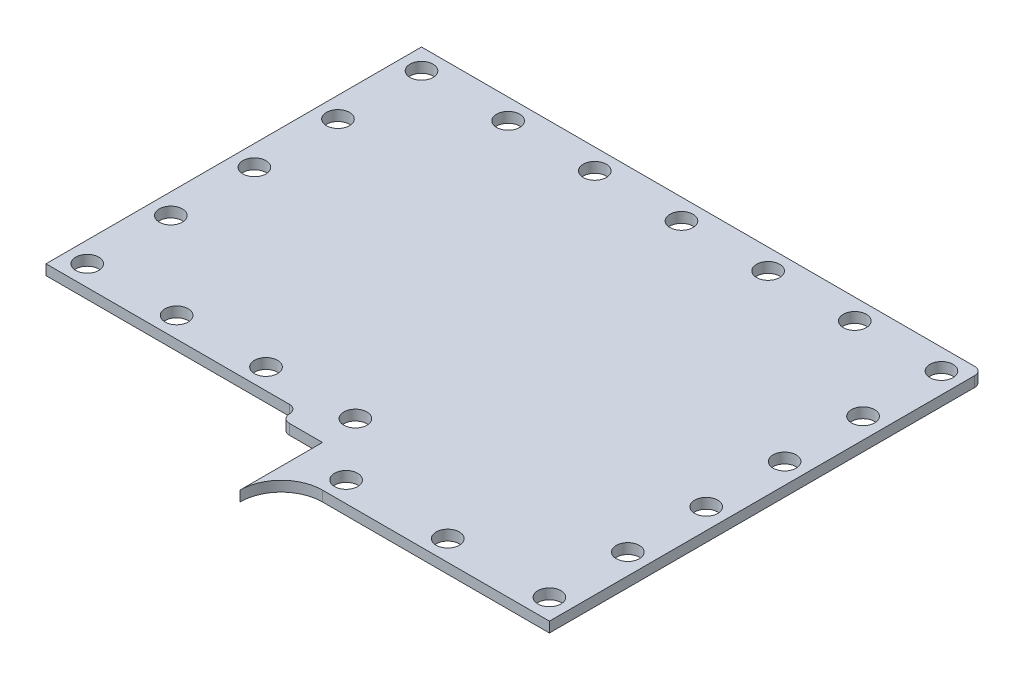
SolidWorks part; units mm, degrees
material "Zoltek Panex 33"
ref_plane "Front Plane" through (0, 0, 0) normal (0, 0, 1) x (1, 0, 0)
ref_plane "Top Plane" through (0, 0, 0) normal (0, 1, 0) x (1, 0, 0)
ref_plane "Right Plane" through (0, 0, 0) normal (1, 0, 0) x (0, 0, -1)
other "Bounding Box"
ref_plane "Default Plane" through (-8.9266, -12.7485, 0) normal (-0.1736, 0.9848, 0) x (0.9848, 0.1736, 0)
sketch "Sketch1" plane through (0, 0, 0) normal (0, 1, 0) x (1, 0, 0)
  line B0 (8.89, -66.675) -> (43.815, -66.675)
  line B1 (43.815, -66.675) -> (43.815, -1.27)
  line B2 (42.545, 0) -> (-42.545, 0)
  line B3 (-42.545, 0) -> (-42.545, -57.785)
  line B4 (-42.545, -57.785) -> (-5.08, -57.785)
  line B5 (-2.54, -60.325) -> (2.54, -60.325)
  line B6 (2.54, -60.325) -> (2.54, -73.025)
  arc B7 (8.89, -66.675) -> (2.54, -73.025) centre (8.89, -73.025) ccw
  arc B8 (43.815, -1.27) -> (42.545, 0) centre (42.5797, -1.2353) ccw
  arc B9 (-5.08, -57.785) -> (-3.81, -59.055) centre (-5.08, -59.055) cw
  arc B10 (-3.81, -59.055) -> (-2.54, -60.325) centre (-2.54, -59.055) ccw
sketch_block_instance "Left side Top plate-1"
sketch_block "Left side Top plate"
extrude "Boss-Extrude1" add sketch "Sketch1" along normal blind 1.5875
sketch "Sketch2" plane through (0, 1.5875, 0) normal (0, 1, 0) x (-1, 0, 0)
  line L0 (-9.3488, 63.5) -> (-40.64, 63.5) construction
  line L1 (-40.64, 63.5) -> (-40.64, 3.175) construction
  line L2 (-40.64, 3.175) -> (39.37, 3.175) construction
  line L3 (39.37, 3.175) -> (39.37, 54.61) construction
  line L4 (39.37, 54.61) -> (-1.8892, 54.61) construction
  line L5 (-1.8892, 54.61) -> (-9.3488, 63.5) construction
  line L6 (-42.545, 0) -> (42.545, 0) construction
  line L7 (42.545, 0) -> (42.545, 57.785) construction
  line L8 (42.545, 57.785) -> (5.08, 57.785) construction
  line L9 (-8.89, 66.675) -> (-43.815, 66.675) construction
  line L10 (-43.815, 66.675) -> (-43.815, 1.27) construction
  circle A0 centre (39.37, 3.175) radius 1.778
  circle A1 centre (26.035, 3.175) radius 1.778
  circle A2 centre (12.7, 3.175) radius 1.778
  circle A3 centre (-0.635, 3.175) radius 1.778
  circle A4 centre (-13.97, 3.175) radius 1.778
  circle A5 centre (-27.305, 3.175) radius 1.778
  circle A6 centre (-40.64, 3.175) radius 1.778
  circle A7 centre (39.37, 16.0338) radius 1.778
  circle A8 centre (39.37, 28.8925) radius 1.778
  circle A9 centre (39.37, 41.7513) radius 1.778
  circle A11 centre (-40.64, 15.24) radius 1.778
  circle A12 centre (-40.64, 27.305) radius 1.778
  circle A13 centre (-40.64, 39.37) radius 1.778
  circle A14 centre (-40.64, 51.435) radius 1.778
  circle A15 centre (-40.64, 63.5) radius 1.778
  circle A16 centre (-24.9944, 63.5) radius 1.778
  circle A17 centre (-9.3488, 63.5) radius 1.778
  circle A18 centre (-1.8892, 54.61) radius 1.778
  circle A19 centre (11.8639, 54.61) radius 1.778
  circle A20 centre (25.6169, 54.61) radius 1.778
  circle A21 centre (39.37, 54.61) radius 1.778
  circle A22 centre (39.37, 54.61) radius 1.778 [skipped]
  dimension "D8" = 3.556
  dimension "D14" = 12.8588
  dimension "D1" = 3.175
  dimension "D2" = 3.175
  dimension "D3" = 3.175
  dimension "D4" = 3.175
  dimension "D5" = 3.175
  dimension "D6" = 3.175
  dimension "D7" = 130
  dimension "D9" = 7
  dimension "D10" = 5
  dimension "D11" = 6
  dimension "D12" = 3
  dimension "D13" = 4
extrude "Cut-Extrude1" cut sketch "Sketch2" against normal through all both and the other way through all
